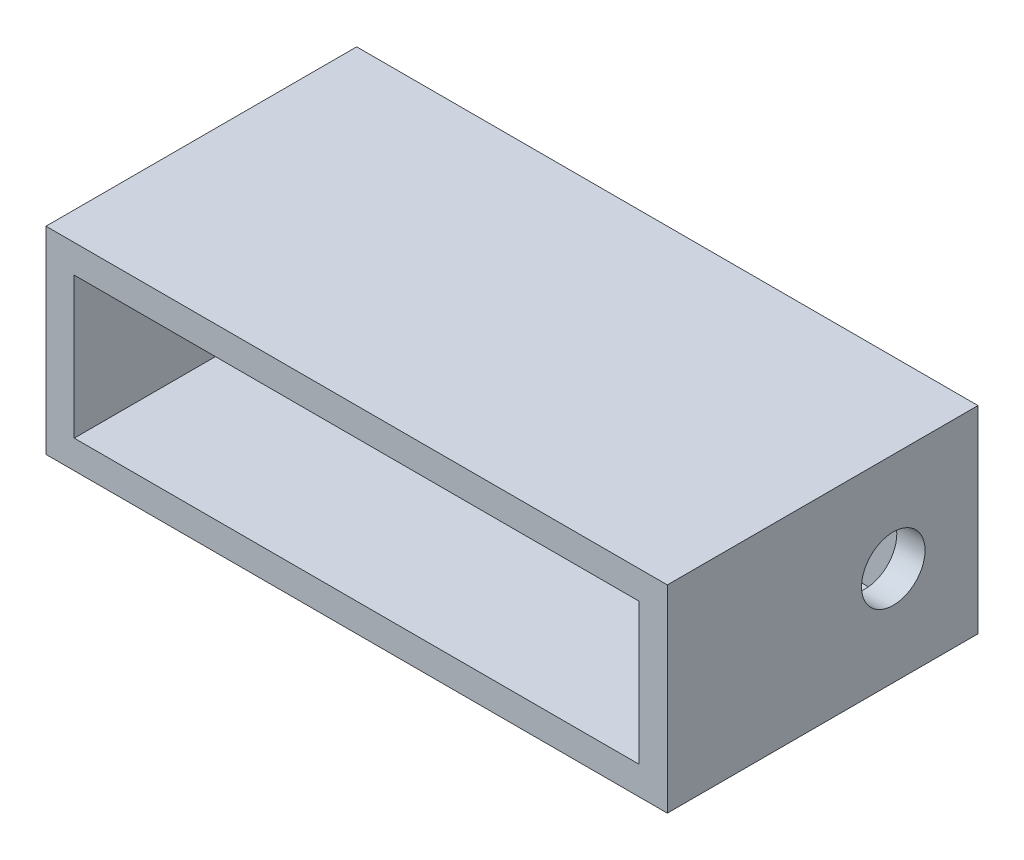
SolidWorks part; units mm, degrees
ref_plane "Plano frontal" through (0, 0, 0) normal (0, 0, 1) x (1, 0, 0)
ref_plane "Plano superior" through (0, 0, 0) normal (0, 1, 0) x (1, 0, 0)
ref_plane "Plano direito" through (0, 0, 0) normal (1, 0, 0) x (0, 0, -1)
sketch "Esboço1" plane through (0, 0, 0) normal (0, 0, 1) x (1, 0, 0)
  line L1 (22, -7) -> (-22, -7)
  line L2 (22, -7) -> (22, 7)
  line L3 (22, 7) -> (-22, 7)
  line L4 (-22, -7) -> (-22, 7)
  line L5 (22, -7) -> (-22, 7) construction
  line L6 (22, 7) -> (-22, -7) construction
  point P0 (0, 0)
  point P6 (0, 0)
  dimension "D1" = 44
  dimension "D2" = 14
extrude "Ressalto-extrusão1" add sketch "Esboço1" along normal blind 22
sketch "Esboço2" plane through (0, 0, 22) normal (0, 0, 1) x (1, 0, 0)
  line L1 (20, -5) -> (-20, -5)
  line L2 (20, -5) -> (20, 5)
  line L3 (20, 5) -> (-20, 5)
  line L4 (-20, -5) -> (-20, 5)
  line L5 (20, -5) -> (-20, 5) construction
  line L6 (20, 5) -> (-20, -5) construction
  point P0 (0, 0)
  dimension "D1" = 40
  dimension "D2" = 10
extrude "Corte-extrusão1" cut sketch "Esboço2" against normal blind 19
sketch "Esboço3" plane through (22, 0, 0) normal (1, 0, 0) x (0, 0, -1)
  line L0 (5.5095, 0) -> (-24.9686, 0) construction
  line L1 (-11, -7) -> (-11, 7) construction
  line L2 (-22, -7) -> (0, -7) construction
  line L3 (-22, 7) -> (0, 7) construction
  line L4 (0, -7) -> (0, 7) construction
  circle A0 centre (-6, 0) radius 2.25
  dimension "D1" = 4.5
  dimension "D2" = 6
extrude "Corte-extrusão2" cut sketch "Esboço3" against normal blind 5
